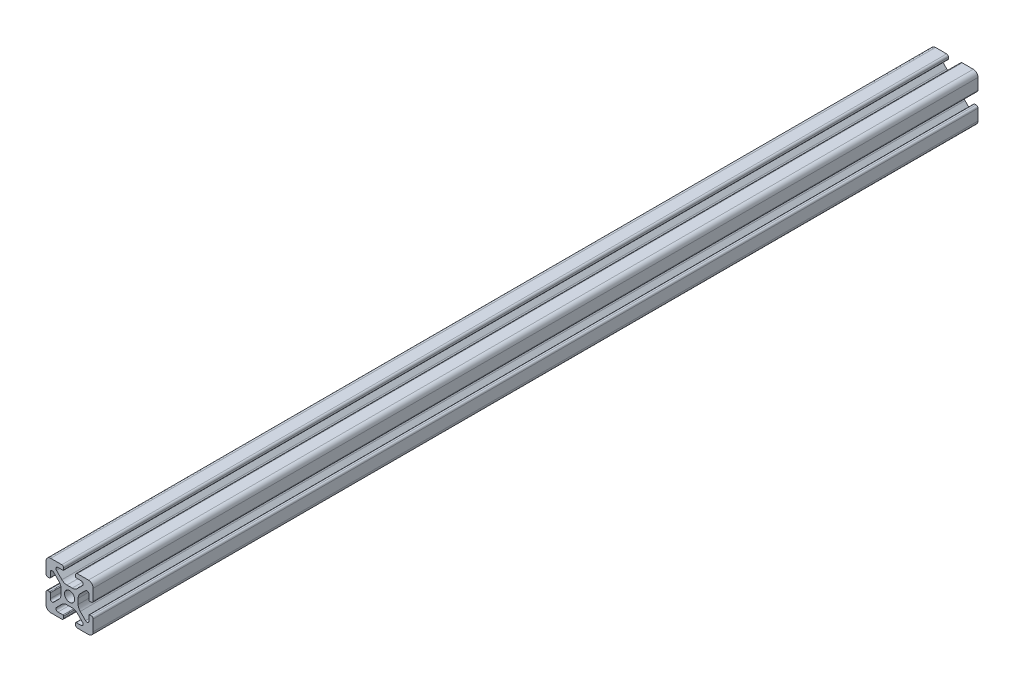
SolidWorks part; units mm, degrees
material "6061-T6 (SS)"
ref_plane "Front Plane" through (0, 0, 0) normal (0, 0, 1) x (1, 0, 0)
ref_plane "Top Plane" through (0, 0, 0) normal (0, 1, 0) x (1, 0, 0)
ref_plane "Right Plane" through (0, 0, 0) normal (1, 0, 0) x (0, 0, -1)
sketch "Sketch1" plane through (0, 0, 0) normal (0, 0, 1) x (1, 0, 0)
  line L2 (-9.9949, 7.9883) -> (-9.9949, 3.2893)
  line L3 (-7.9883, 9.9949) -> (-3.2893, 9.9949)
  line L4 (-2.5019, 9.2075) -> (-2.5019, 8.4963)
  line L5 (-2.8067, 8.1915) -> (-4.9149, 8.1915)
  line L6 (-5.5076, 6.7606) -> (-3.2528, 4.5058)
  line L7 (-6.7606, 5.5076) -> (-4.5058, 3.2528)
  line L8 (-8.1915, 4.9149) -> (-8.1915, 2.8067)
  line L9 (-8.4963, 2.5019) -> (-9.2075, 2.5019)
  line L11 (-1.1334, 3.6279) -> (1.1334, 3.6279)
  line L12 (-3.6279, 1.1334) -> (-3.6279, -1.1334)
  line L13 (8.4963, 2.5019) -> (9.2075, 2.5019)
  line L14 (8.1915, 4.9149) -> (8.1915, 2.8067)
  line L15 (9.9949, 7.9883) -> (9.9949, 3.2893)
  line L16 (7.9883, 9.9949) -> (3.2893, 9.9949)
  line L17 (2.5019, 9.2075) -> (2.5019, 8.4963)
  line L18 (2.8067, 8.1915) -> (4.9149, 8.1915)
  line L19 (3.6279, 1.1334) -> (3.6279, -1.1334)
  line L20 (5.5076, 6.7606) -> (3.2528, 4.5058)
  line L21 (6.7606, 5.5076) -> (4.5058, 3.2528)
  line L22 (-8.4963, -2.5019) -> (-9.2075, -2.5019)
  line L23 (-8.1915, -4.9149) -> (-8.1915, -2.8067)
  line L24 (-6.7606, -5.5076) -> (-4.5058, -3.2528)
  line L25 (-5.5076, -6.7606) -> (-3.2528, -4.5058)
  line L26 (-2.8067, -8.1915) -> (-4.9149, -8.1915)
  line L27 (-2.5019, -9.2075) -> (-2.5019, -8.4963)
  line L28 (-7.9883, -9.9949) -> (-3.2893, -9.9949)
  line L29 (-9.9949, -7.9883) -> (-9.9949, -3.2893)
  line L30 (9.9949, -7.9883) -> (9.9949, -3.2893)
  line L31 (7.9883, -9.9949) -> (3.2893, -9.9949)
  line L32 (2.5019, -9.2075) -> (2.5019, -8.4963)
  line L33 (2.8067, -8.1915) -> (4.9149, -8.1915)
  line L34 (5.5076, -6.7606) -> (3.2528, -4.5058)
  line L35 (6.7606, -5.5076) -> (4.5058, -3.2528)
  line L36 (8.1915, -4.9149) -> (8.1915, -2.8067)
  line L37 (8.4963, -2.5019) -> (9.2075, -2.5019)
  line L38 (-1.1334, -3.6279) -> (1.1334, -3.6279)
  circle A0 centre (0, 0) radius 2.1463
  arc A1 (-9.9949, 7.9883) -> (-7.9883, 9.9949) centre (-7.9883, 7.9883) cw
  arc A2 (-6.7606, 5.5076) -> (-8.1915, 4.9149) centre (-7.3533, 4.9149) ccw
  arc A3 (-4.9149, 8.1915) -> (-5.5076, 6.7606) centre (-4.9149, 7.3533) ccw
  arc A4 (-3.2893, 9.9949) -> (-2.5019, 9.2075) centre (-3.2893, 9.2075) cw
  arc A5 (-9.9949, 3.2893) -> (-9.2075, 2.5019) centre (-9.2075, 3.2893) ccw
  arc A6 (-8.1915, 2.8067) -> (-8.4963, 2.5019) centre (-8.4963, 2.8067) cw
  arc A7 (-2.5019, 8.4963) -> (-2.8067, 8.1915) centre (-2.8067, 8.4963) cw
  arc A8 (-1.1334, 3.6279) -> (-3.2528, 4.5058) centre (-1.1334, 6.6251) cw
  arc A9 (-3.6279, 1.1334) -> (-4.5058, 3.2528) centre (-6.6251, 1.1334) ccw
  arc A10 (8.1915, 2.8067) -> (8.4963, 2.5019) centre (8.4963, 2.8067) ccw
  arc A11 (9.9949, 3.2893) -> (9.2075, 2.5019) centre (9.2075, 3.2893) cw
  arc A12 (9.9949, 7.9883) -> (7.9883, 9.9949) centre (7.9883, 7.9883) ccw
  arc A13 (3.2893, 9.9949) -> (2.5019, 9.2075) centre (3.2893, 9.2075) ccw
  arc A14 (2.5019, 8.4963) -> (2.8067, 8.1915) centre (2.8067, 8.4963) ccw
  arc A15 (1.1334, 3.6279) -> (3.2528, 4.5058) centre (1.1334, 6.6251) ccw
  arc A16 (3.6279, 1.1334) -> (4.5058, 3.2528) centre (6.6251, 1.1334) cw
  arc A17 (6.7606, 5.5076) -> (8.1915, 4.9149) centre (7.3533, 4.9149) cw
  arc A18 (4.9149, 8.1915) -> (5.5076, 6.7606) centre (4.9149, 7.3533) cw
  arc A19 (-3.6279, -1.1334) -> (-4.5058, -3.2528) centre (-6.6251, -1.1334) cw
  arc A20 (-1.1334, -3.6279) -> (-3.2528, -4.5058) centre (-1.1334, -6.6251) ccw
  arc A21 (-2.5019, -8.4963) -> (-2.8067, -8.1915) centre (-2.8067, -8.4963) ccw
  arc A22 (-8.1915, -2.8067) -> (-8.4963, -2.5019) centre (-8.4963, -2.8067) ccw
  arc A23 (-9.9949, -3.2893) -> (-9.2075, -2.5019) centre (-9.2075, -3.2893) cw
  arc A24 (-3.2893, -9.9949) -> (-2.5019, -9.2075) centre (-3.2893, -9.2075) ccw
  arc A25 (-4.9149, -8.1915) -> (-5.5076, -6.7606) centre (-4.9149, -7.3533) cw
  arc A26 (-6.7606, -5.5076) -> (-8.1915, -4.9149) centre (-7.3533, -4.9149) cw
  arc A27 (-9.9949, -7.9883) -> (-7.9883, -9.9949) centre (-7.9883, -7.9883) ccw
  arc A28 (9.9949, -7.9883) -> (7.9883, -9.9949) centre (7.9883, -7.9883) cw
  arc A29 (6.7606, -5.5076) -> (8.1915, -4.9149) centre (7.3533, -4.9149) ccw
  arc A30 (4.9149, -8.1915) -> (5.5076, -6.7606) centre (4.9149, -7.3533) ccw
  arc A31 (3.2893, -9.9949) -> (2.5019, -9.2075) centre (3.2893, -9.2075) cw
  arc A32 (9.9949, -3.2893) -> (9.2075, -2.5019) centre (9.2075, -3.2893) ccw
  arc A33 (8.1915, -2.8067) -> (8.4963, -2.5019) centre (8.4963, -2.8067) cw
  arc A34 (2.5019, -8.4963) -> (2.8067, -8.1915) centre (2.8067, -8.4963) cw
  arc A35 (1.1334, -3.6279) -> (3.2528, -4.5058) centre (1.1334, -6.6251) cw
  arc A36 (3.6279, -1.1334) -> (4.5058, -3.2528) centre (6.6251, -1.1334) ccw
extrude "Boss-Extrude1" add sketch "Sketch1" along normal mid plane 375
